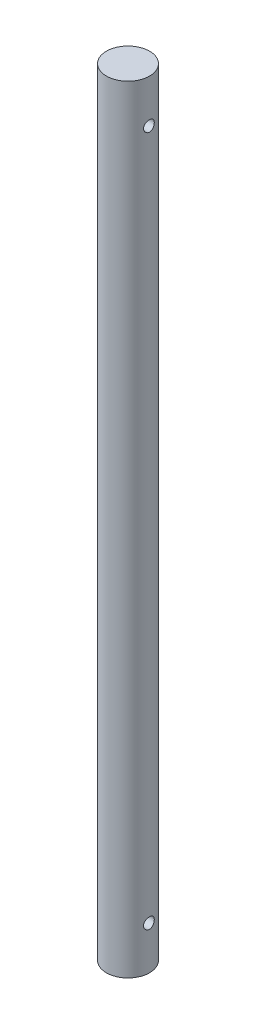
SolidWorks part; units mm, degrees
ref_plane "Front Plane" through (0, 0, 0) normal (0, 0, 1) x (1, 0, 0)
ref_plane "Top Plane" through (0, 0, 0) normal (0, 1, 0) x (1, 0, 0)
ref_plane "Right Plane" through (0, 0, 0) normal (1, 0, 0) x (0, 0, -1)
sketch "Sketch1" plane through (0, 0, 0) normal (0, 1, 0) x (1, 0, 0)
  circle A0 centre (0, 0) radius 25.4
  dimension "D1" = 50.8
extrude "Boss-Extrude1" add sketch "Sketch1" along normal blind 914.4
sketch "Sketch2" plane through (0, 0, 0) normal (1, 0, 0) x (0, 0, -1)
  line L0 (25.4, 914.4) -> (-25.4, 914.4) construction
  line L1 (-25.4, 0) -> (25.4, 0) construction
  circle A0 centre (0, 863.6) radius 6.35
  circle A1 centre (0, 50.8) radius 6.35
  dimension "D1" = 12.7
  dimension "D2" = 50.8
  dimension "D3" = 12.7
  dimension "D4" = 50.8
extrude "Cut-Extrude3" cut sketch "Sketch2" against normal through all both and the other way through all
